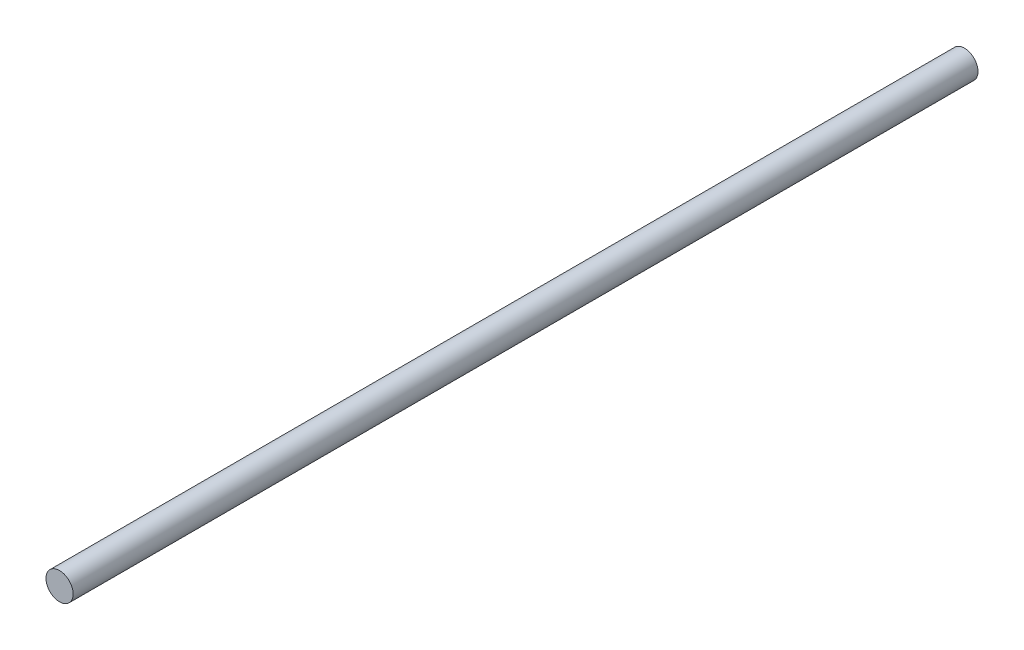
SolidWorks part; units mm, degrees
ref_plane "Front Plane" through (0, 0, 0) normal (0, 0, 1) x (1, 0, 0)
ref_plane "Top Plane" through (0, 0, 0) normal (0, 1, 0) x (1, 0, 0)
ref_plane "Right Plane" through (0, 0, 0) normal (1, 0, 0) x (0, 0, -1)
sketch "Sketch1" plane through (0, 0, 0) normal (0, 0, 1) x (1, 0, 0)
  circle A0 centre (0, 0) radius 3
extrude "Boss-Extrude1" add sketch "Sketch1" against normal blind 200
